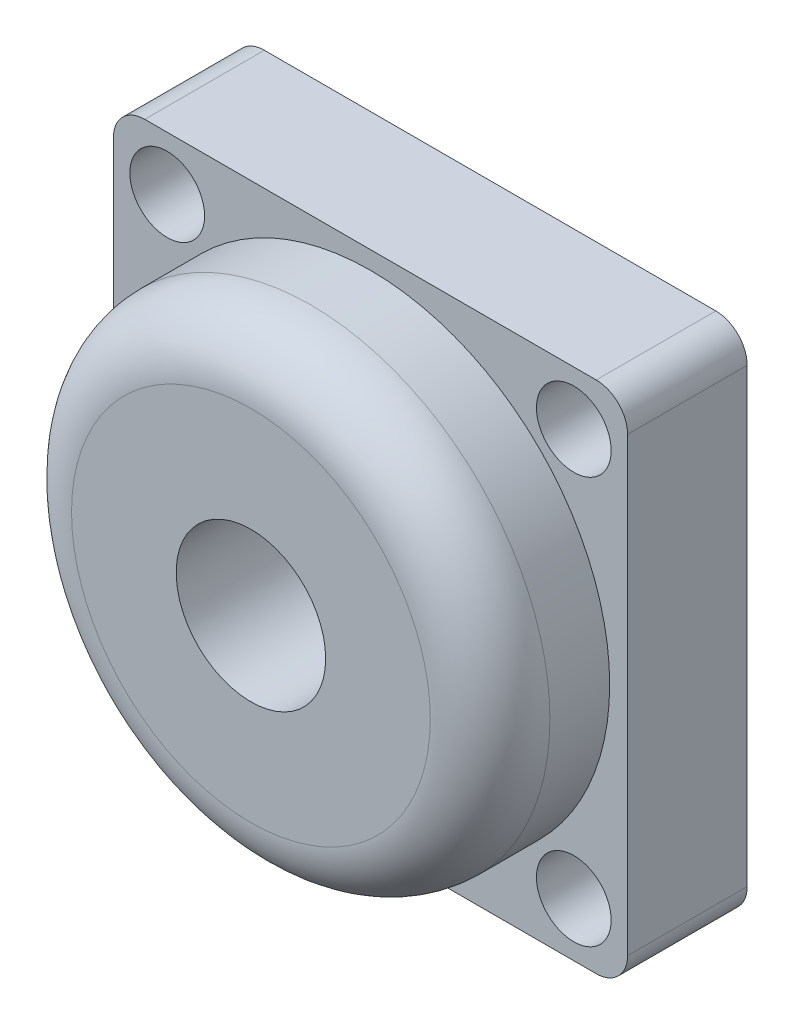
SolidWorks part; units mm, degrees
ref_plane "Front Plane" through (0, 0, 0) normal (0, 0, 1) x (1, 0, 0)
ref_plane "Top Plane" through (0, 0, 0) normal (0, 1, 0) x (1, 0, 0)
ref_plane "Right Plane" through (0, 0, 0) normal (1, 0, 0) x (0, 0, -1)
sketch "Sketch1" plane through (0, 0, 0) normal (0, 0, 1) x (1, 0, 0)
  line L1 (37.75, -43) -> (-37.75, -43)
  line L2 (43, -37.75) -> (43, 37.75)
  line L3 (37.75, 43) -> (-37.75, 43)
  line L4 (-43, -37.75) -> (-43, 37.75)
  line L5 (43, -43) -> (-43, 43) construction
  line L6 (43, 43) -> (-43, -43) construction
  arc A0 (43, 37.75) -> (37.75, 43) centre (37.75, 37.75) ccw
  arc A1 (37.75, -43) -> (43, -37.75) centre (37.75, -37.75) ccw
  arc A2 (-37.75, -43) -> (-43, -37.75) centre (-37.75, -37.75) cw
  arc A3 (-37.75, 43) -> (-43, 37.75) centre (-37.75, 37.75) ccw
  point P0 (0, 0)
  dimension "D3" = 5.25
  dimension "D1" = 86
  dimension "D2" = 86
extrude "Boss-Extrude1" add sketch "Sketch1" along normal blind 20
sketch "Sketch2" plane through (0, 0, 20) normal (0, 0, 1) x (1, 0, 0)
  circle A0 centre (0, 0) radius 40
  dimension "D1" = 80
extrude "Boss-Extrude2" add sketch "Sketch2" along normal blind 20
sketch "Sketch3" plane through (0, 0, 40) normal (0, 0, 1) x (1, 0, 0)
  line L3 (37.75, 43) -> (-37.75, 43) construction
  line L4 (-43, 37.75) -> (-43, -37.75) construction
  line L5 (-37.75, -43) -> (37.75, -43) construction
  line L6 (43, -37.75) -> (43, 37.75) construction
  circle A0 centre (0, 0) radius 12.5
  circle A1 centre (-34, 34) radius 6.25
  circle A2 centre (34, 34) radius 6.25
  circle A3 centre (34, -34) radius 6.25
  circle A4 centre (-34, -34) radius 6.25
  dimension "D1" = 25
  dimension "D2" = 12.5
  dimension "D5" = 9
  dimension "D3" = 9
  dimension "D4" = 9
  dimension "D6" = 9
  dimension "D7" = 9
  dimension "D8" = 9
  dimension "D9" = 9
  dimension "D10" = 9
extrude "Cut-Extrude1" cut sketch "Sketch3" against normal through all
fillet "Fillet1" radius 10 1 edges at (40, 0, 40)
